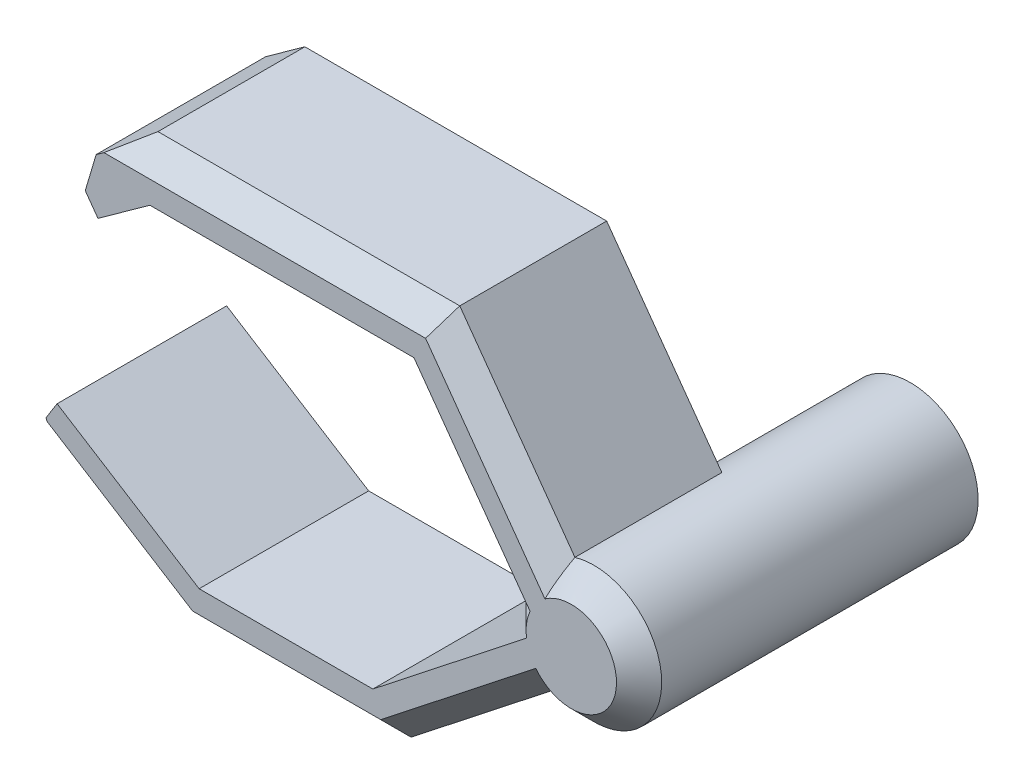
SolidWorks part; units mm, degrees
ref_plane "Front Plane" through (0, 0, 0) normal (0, 0, 1) x (1, 0, 0)
ref_plane "Top Plane" through (0, 0, 0) normal (0, 1, 0) x (1, 0, 0)
ref_plane "Right Plane" through (0, 0, 0) normal (1, 0, 0) x (0, 0, -1)
sketch "Sketch1" plane through (0, 0, 0) normal (0, 0, 1) x (1, 0, 0)
  circle A0 centre (0, 0) radius 6
  dimension "D1" = 12
extrude "Boss-Extrude1" add sketch "Sketch1" along normal blind 15
sketch "Sketch2" plane through (0, 0, 15) normal (0, 0, 1) x (1, 0, 0)
  line L0 (0, 0) -> (-12.8949, 17.9392) construction
  line L1 (-12.8949, 17.9392) -> (-37.9322, 17.9392) construction
  line L2 (-37.9322, 17.9392) -> (-42.9753, 14.3142) construction
  line L3 (0, 0) -> (-16.8678, -13.2703) construction
  line L4 (-16.8678, -13.2703) -> (-33.5081, -13.2703) construction
  line L5 (-33.5081, -13.2703) -> (-46.3878, -5.1816) construction
  line L6 (-34.084, -15.2703) -> (-45.137, -8.3289)
  line L7 (-16.1754, -15.2703) -> (-34.084, -15.2703)
  line L8 (2.7418, -0.3877) -> (-16.1754, -15.2703)
  line L9 (2.7418, -0.3877) -> (-11.8694, 19.9392)
  line L10 (-11.8694, 19.9392) -> (-38.5765, 19.9392)
  line L11 (-38.5765, 19.9392) -> (-42.0437, 17.4469)
  line L12 (-32.9321, -11.2703) -> (-45.5007, -3.377)
  line L13 (-17.5603, -11.2703) -> (-32.9321, -11.2703)
  line L14 (-2.7418, 0.3877) -> (-17.5603, -11.2703)
  line L15 (-2.7418, 0.3877) -> (-13.9203, 15.9392)
  line L16 (-13.9203, 15.9392) -> (-37.288, 15.9392)
  line L17 (-37.288, 15.9392) -> (-41.8852, 12.6347)
  line L18 (-42.0437, 17.4469) -> (-43.0096, 14.199)
  line L19 (-43.0096, 14.199) -> (-41.8852, 12.6347)
  line L20 (-45.137, -8.3289) -> (-46.4832, -4.9415)
  line L21 (-46.4832, -4.9415) -> (-45.5007, -3.377)
  line L22 (-32.9321, -11.2703) -> (-43.0096, -4.9415) construction
  line L23 (-37.288, 15.9392) -> (-39.7091, 14.199) construction
  line L24 (-33.5081, -13.2703) -> (-44.0733, -6.6352) construction
  line L25 (-37.9322, 17.9392) -> (-40.8764, 15.8229) construction
  dimension "D1" = 2
  dimension "D2" = 2
extrude "Boss-Extrude2" add sketch "Sketch2" against normal blind 15
chamfer "Chamfer1" distance 2 angle 45 7 edges at (-5.9409, 0.8401, 15) (-39.6105, -11.7996, 15) (-25.1297, -15.2703, 15) (-9.6923, -10.17, 15) (5.9409, -0.8401, 15) (-6.7736, 12.8499, 15) (-25.2229, 19.9392, 15)
sketch "Sketch3" plane through (0, 0, 0) normal (0, 0, -1) x (-1, 0, 0)
  circle A0 centre (0, 0) radius 6
extrude "Boss-Extrude3" add sketch "Sketch3" along normal blind 15
